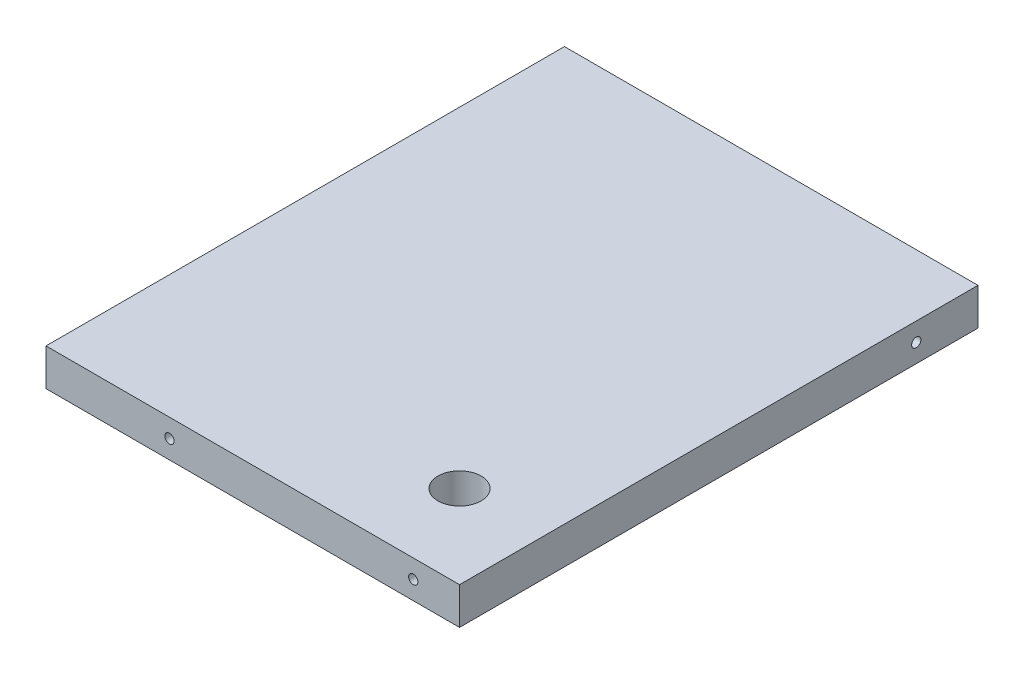
SolidWorks part; units mm, degrees
ref_plane "Front Plane" through (0, 0, 0) normal (0, 0, 1) x (1, 0, 0)
ref_plane "Top Plane" through (0, 0, 0) normal (0, 1, 0) x (1, 0, 0)
ref_plane "Right Plane" through (0, 0, 0) normal (1, 0, 0) x (0, 0, -1)
sketch "Sketch1" plane through (0, 0, 0) normal (0, 1, 0) x (1, 0, 0)
  line L0 (-87.8942, 44.2567) -> (-87.8942, 212.2567) construction
  line L1 (-154.8942, 212.2567) -> (-20.8942, 212.2567)
  line L2 (-154.8942, 212.2567) -> (-154.8942, 44.2567)
  line L3 (-154.8942, 44.2567) -> (-20.8942, 44.2567)
  line L4 (-20.8942, 212.2567) -> (-20.8942, 44.2567)
  circle A0 centre (-47.8942, 71.2567) radius 7
  dimension "D3" = 27
  dimension "D1" = 134
  dimension "D2" = 168
  dimension "D4" = 27
extrude "Boss-Extrude1" add sketch "Sketch1" along normal blind 12
sketch "Sketch2" plane through (0, 0, 0) normal (0, 0, 1) x (1, 0, 0)
  line L0 (-154.8942, 6) -> (-20.8942, 6) construction
  line L1 (-154.8942, 12) -> (-154.8942, 0) construction
  line L2 (-20.8942, 12) -> (-20.8942, 0) construction
  circle A0 centre (-114.8942, 6) radius 1.5
  circle A1 centre (-35.8942, 6) radius 1.5
  dimension "D1" = 3
  dimension "D2" = 3
  dimension "D3" = 40
  dimension "D4" = 15
extrude "Cut-Extrude1" cut sketch "Sketch2" against normal blind 20 from surface at -44.2567 starting at face at (-87.8942, 6, -44.2567)
sketch "Sketch3" plane through (0, 0, 0) normal (1, 0, 0) x (0, 0, -1)
  line L0 (44.2567, 6) -> (213.3169, 6) construction
  line L1 (44.2567, 12) -> (44.2567, 0) construction
  circle A0 centre (192.2567, 6) radius 1.5
  dimension "D1" = 3
  dimension "D2" = 20
extrude "Cut-Extrude2" cut sketch "Sketch3" against normal blind 20 from surface at -20.8942 starting at face at (-20.8942, 6, -128.2567)
